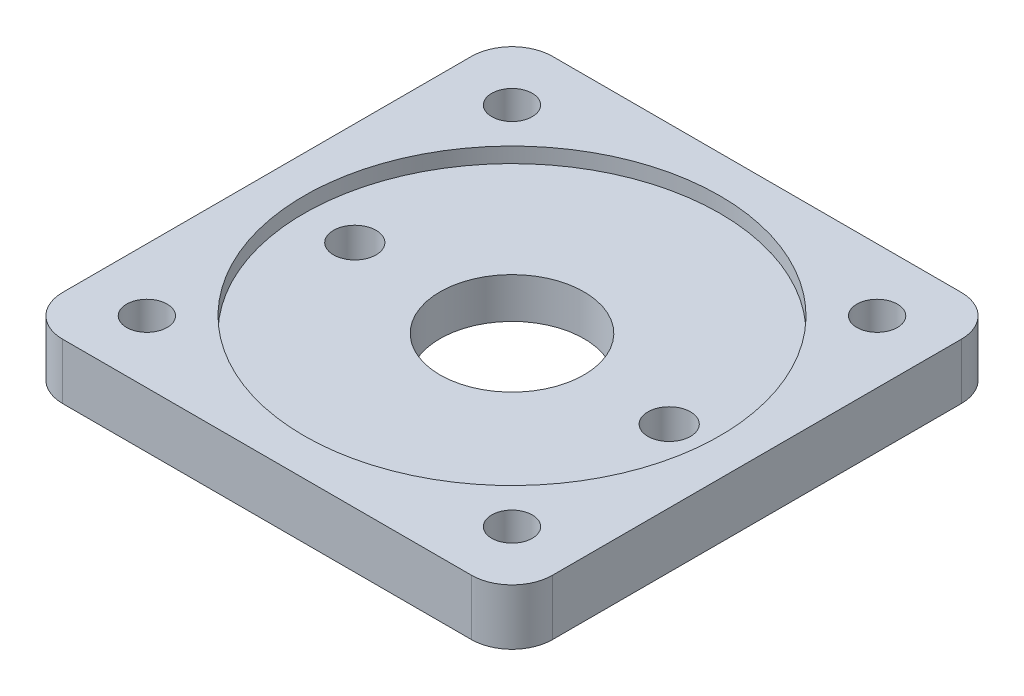
SolidWorks part; units mm, degrees
ref_plane "Ön Düzlem" through (0, 0, 0) normal (0, 0, 1) x (1, 0, 0)
ref_plane "Üst Düzlem" through (0, 0, 0) normal (0, 1, 0) x (1, 0, 0)
ref_plane "Sağ Düzlem" through (0, 0, 0) normal (1, 0, 0) x (0, 0, -1)
sketch "Çizim2" plane through (0, 0, 0) normal (0, 1, 0) x (1, 0, 0)
  line L1 (-20.15, -24.15) -> (20.15, -24.15)
  line L2 (-24.15, -20.15) -> (-24.15, 20.15)
  line L3 (-20.15, 24.15) -> (20.15, 24.15)
  line L4 (24.15, -20.15) -> (24.15, 20.15)
  line L5 (-24.15, -24.15) -> (24.15, 24.15) construction
  line L6 (-24.15, 24.15) -> (24.15, -24.15) construction
  circle A0 centre (0, 0) radius 7.1
  circle A1 centre (-18, 18) radius 2
  circle A2 centre (18, 18) radius 2
  circle A3 centre (-18, -18) radius 2
  circle A4 centre (18, -18) radius 2
  arc A5 (-20.15, -24.15) -> (-24.15, -20.15) centre (-20.15, -20.15) cw
  arc A6 (20.15, -24.15) -> (24.15, -20.15) centre (20.15, -20.15) ccw
  arc A7 (20.15, 24.15) -> (24.15, 20.15) centre (20.15, 20.15) cw
  arc A8 (-24.15, 20.15) -> (-20.15, 24.15) centre (-20.15, 20.15) cw
  circle A9 centre (-15.5, 0) radius 2.1
  circle A10 centre (15.5, 0) radius 2.1
  point P0 (0, 0)
  dimension "D2" = 14.2
  dimension "D3" = 4
  dimension "D4" = 36
  dimension "D5" = 36
  dimension "D6" = 4
  dimension "D7" = 15.5
  dimension "D8" = 31
  dimension "D9" = 4.2
  dimension "D1" = 48.3
extrude "Yükseklik-Ekstrüzyon1" add sketch "Çizim2" along normal blind 5.5
sketch "Çizim3" plane through (0, 5.5, 0) normal (0, 1, 0) x (1, 0, 0)
  circle A0 centre (0, 0) radius 20.5
  dimension "D1" = 41
extrude "Kes-Ekstrüzyon1" cut sketch "Çizim3" against normal blind 1.5
